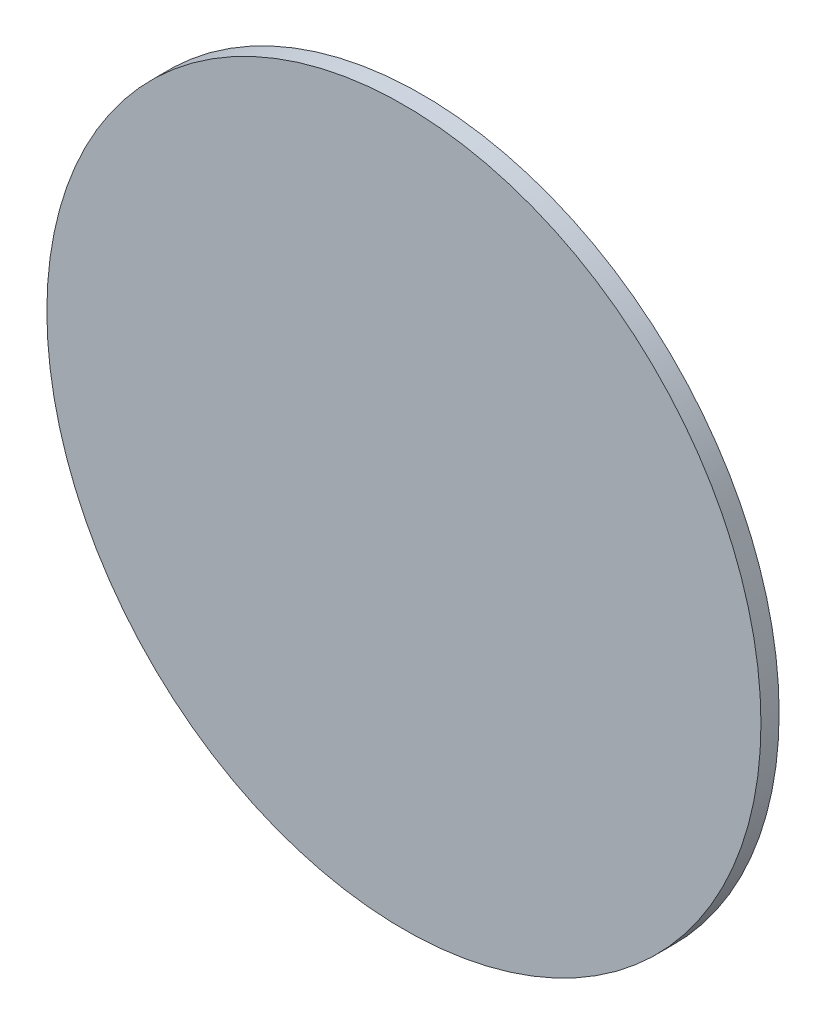
SolidWorks part; units mm, degrees
material "Barium"
ref_plane "Front" through (0, 0, 0) normal (0, 0, 1) x (1, 0, 0)
ref_plane "Top" through (0, 0, 0) normal (0, 1, 0) x (1, 0, 0)
ref_plane "Right" through (0, 0, 0) normal (1, 0, 0) x (0, 0, -1)
sketch "Sketch1" plane through (0, 0, 0) normal (0, 0, 1) x (1, 0, 0)
  circle A0 centre (0, 0) radius 133.5
extrude "Boss-Extrude1" add sketch "Sketch1" along normal blind 6.8
